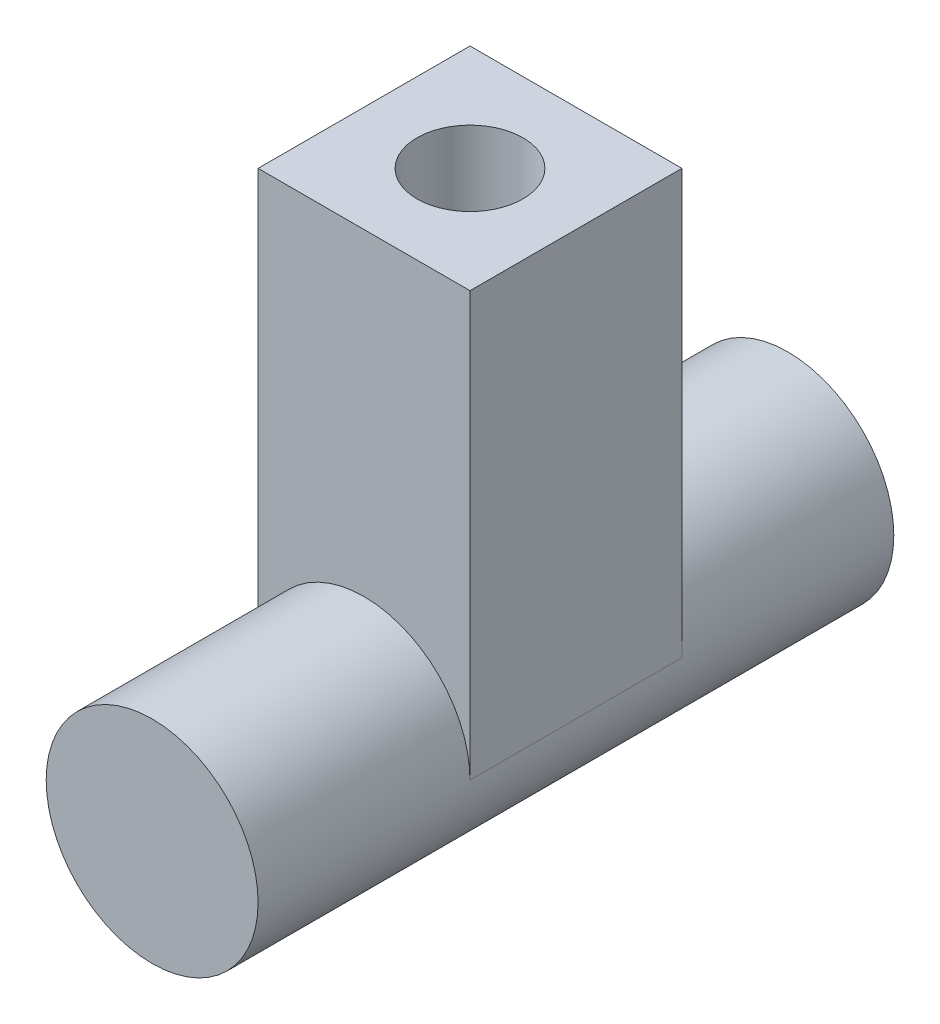
SolidWorks part; units mm, degrees
ref_plane "Front Plane" through (0, 0, 0) normal (0, 0, 1) x (1, 0, 0)
ref_plane "Top Plane" through (0, 0, 0) normal (0, 1, 0) x (1, 0, 0)
ref_plane "Right Plane" through (0, 0, 0) normal (1, 0, 0) x (0, 0, -1)
sketch "Sketch2" plane through (0, 0, 0) normal (0, 0, 1) x (1, 0, 0)
  circle A0 centre (0, 0) radius 10
  dimension "D1" = 20
extrude "Boss-Extrude1" add sketch "Sketch2" along normal mid plane 60
sketch "Sketch3" plane through (0, 0, 0) normal (0, 1, 0) x (1, 0, 0)
  line L1 (-10, 10) -> (10, 10)
  line L2 (-10, 10) -> (-10, -10)
  line L3 (-10, -10) -> (10, -10)
  line L4 (10, 10) -> (10, -10)
  line L5 (-10, 10) -> (10, -10) construction
  line L6 (-10, -10) -> (10, 10) construction
  point P0 (0, 0)
  dimension "D1" = 20
extrude "Boss-Extrude2" add sketch "Sketch3" along normal blind 40
sketch "Sketch4" plane through (0, 40, 0) normal (0, 1, 0) x (1, 0, 0)
  circle A0 centre (0, 0) radius 5
  dimension "D1" = 10
extrude "Cut-Extrude1" cut sketch "Sketch4" against normal blind 10
